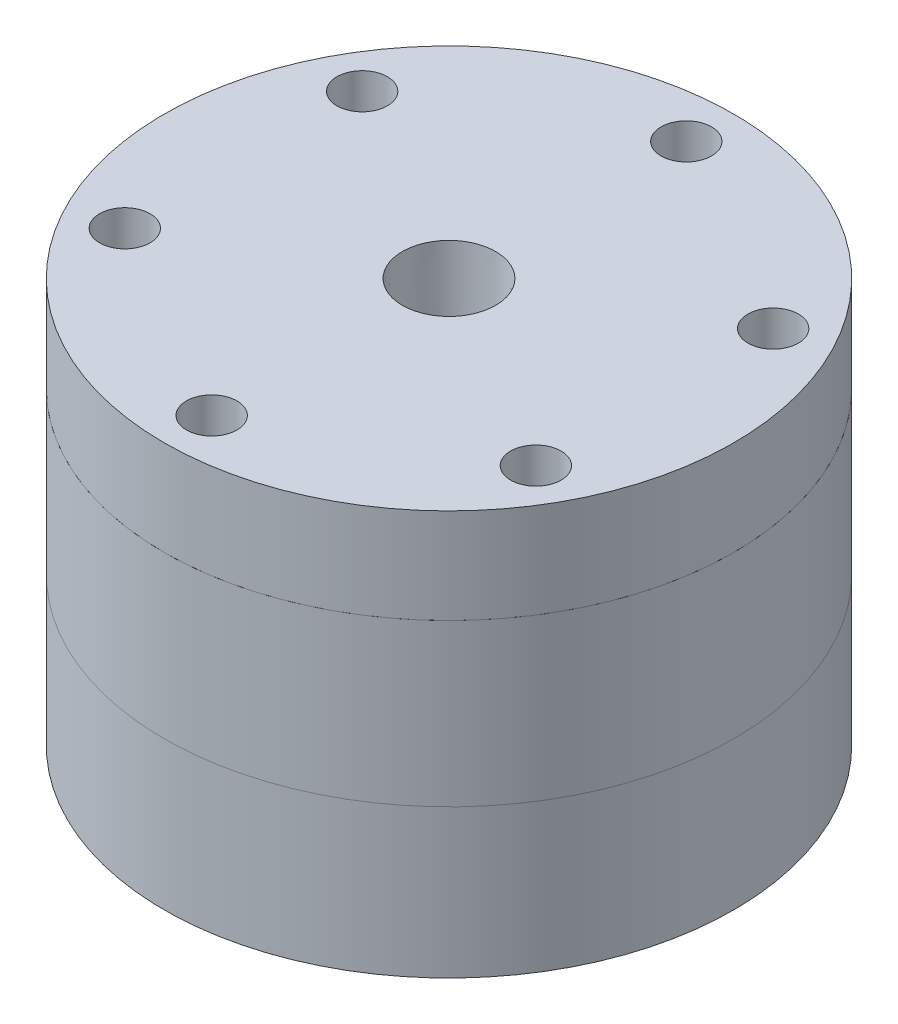
SolidWorks part; units mm, degrees
material "6061-T6 (SS)"
ref_plane "Front Plane" through (0, 0, 0) normal (0, 0, 1) x (1, 0, 0)
ref_plane "Top Plane" through (0, 0, 0) normal (0, 1, 0) x (1, 0, 0)
ref_plane "Right Plane" through (0, 0, 0) normal (1, 0, 0) x (0, 0, -1)
ref_axis "Axis1" through (0, -86.75, 0) along (0, 1, 0)
sketch "Sketch1" plane through (0, 0, 0) normal (0, 0, 1) x (1, 0, 0)
  line L12 (-25.5524, 0) -> (-38.1, 0)
  line L13 (-25.5524, 0) -> (-25.5524, -2.6924)
  line L14 (-25.5524, -2.6924) -> (-21.4884, -2.6924)
  line L15 (-21.4884, -2.6924) -> (-21.4884, 0)
  line L16 (-21.4884, 0) -> (-15.875, 0)
  line L18 (-15.875, 0) -> (-15.875, -15.24)
  line L35 (-38.1, -21.59) -> (-38.1, 0)
  line L36 (0, -86.75) -> (0, 23.25) construction
  line L37 (-15.875, -15.24) -> (-10.795, -15.24)
  line L38 (-10.795, -15.24) -> (-7.62, -18.415)
  line L39 (-7.62, -18.415) -> (-7.62, -21.59)
  line L40 (-7.62, -21.59) -> (-8.9027, -21.59)
  line L41 (-8.9027, -21.59) -> (-8.9027, -19.6088)
  line L42 (-8.9027, -19.6088) -> (-11.9761, -19.6088)
  line L43 (-11.9761, -19.6088) -> (-11.9761, -21.59)
  line L44 (-11.9761, -21.59) -> (-21.4884, -21.59)
  line L45 (-21.4884, -21.59) -> (-21.4884, -18.8976)
  line L46 (-21.4884, -18.8976) -> (-25.5524, -18.8976)
  line L47 (-25.5524, -18.8976) -> (-25.5524, -21.59)
  line L48 (-25.5524, -21.59) -> (-38.1, -21.59)
  dimension "D2" = 1.9812
  dimension "D3" = 15.24
  dimension "D4" = 15.875
  dimension "D5" = 38.1
  dimension "D6" = 25.5524
  dimension "D7" = 3.0734
  dimension "D8" = 11.9761
  dimension "D9" = 7.62
  dimension "D10" = 135
  dimension "D11" = 4.064
  dimension "D12" = 2.6924
  dimension "D13" = 6.35
  dimension "D14" = 3.175
  dimension "D15" = 2.6924
  dimension "D16" = 4.064
revolve "Revolve1" add sketch "Sketch1" angle 360 about axis through (0, -86.75, 0) along (0, 1, 0)
sketch "Sketch21" plane through (0, 0, 0) normal (0, 0, 1) x (1, 0, 0)
  line L19 (-38.1, -35.0774) -> (-38.1, -21.59)
  line L20 (-38.1, -21.59) -> (-19.05, -21.59)
  line L21 (-11.9761, -21.59) -> (-21.4884, -21.59) construction
  line L22 (-19.05, -21.59) -> (-19.05, -35.0774)
  line L25 (-19.05, -35.0774) -> (-38.1, -35.0774)
  line L26 (0, -86.75) -> (0, 23.25) construction
  dimension "D1" = 19.05
  dimension "D3" = 13.4874
revolve "Revolve7" add sketch "Sketch21" angle 360 about axis through (0, -86.75, 0) along (0, 1, 0)
sketch "Sketch4" plane through (0, 0, 0) normal (0, 0, 1) x (1, 0, 0)
  line L0 (-6.35, -35.0774) -> (-38.1, -35.0774)
  line L3 (-11.1125, -41.4274) -> (-6.35, -36.6649)
  line L6 (-38.1, -41.4274) -> (-11.1125, -41.4274)
  line L7 (-6.35, -36.6649) -> (-6.35, -35.0774)
  line L8 (0, -86.75) -> (0, 23.25) construction
  line L9 (-38.1, -41.4274) -> (-38.1, -35.0774)
  dimension "D1" = 6.35
  dimension "D2" = 6.35
  dimension "D3" = 135
  dimension "D4" = 1.5875
revolve "Revolve5" add sketch "Sketch4" angle 360 about axis through (0, -86.75, 0) along (0, 1, 0)
sketch "Sketch13" plane through (0, 0, 0) normal (0, 1, 0) x (1, 0, 0)
  circle A0 centre (0, 0) radius 38.1
extrude "Boss-Extrude1" add sketch "Sketch13" along normal blind 12.7 separate body
ref_plane "Plane1" through (-38.1, 0, 0) normal (-1, 0, 0) x (0, 0, 1)
hole_wizard "1/4 NPT Tapped Hole3" positions "Sketch9" profile "Sketch10" size "1/4" standard "ANSI Inch"
sketch "Sketch9" plane through (-38.1, 0, 0) normal (-1, 0, 0) x (0, 0, 1)
  line L0 (0, -86.75) -> (0, 23.25) construction
  line L2 (0, -35.0774) -> (0, -21.59) construction
  point P0 (0, -30.6324)
  dimension "D1" = 4.445
sketch "Sketch10" plane through (-38.1, -30.6324, 0) normal (0, 1, 0) x (0, 0, 1)
  line L0 (0, 0) -> (0, 25.6943)
  line L1 (5.5626, 22.352) -> (0, 25.6943)
  line L2 (-5.5626, 22.352) -> (0, 25.6943) construction
  line L3 (5.5626, 22.352) -> (5.5626, 9.906)
  line L4 (5.5626, 9.906) -> (5.9437, 9.906)
  line L5 (5.9437, 9.906) -> (6.2403, 0)
  line L6 (-5.9437, 9.906) -> (-6.2403, 0) construction
  line L7 (6.2403, 0) -> (0, 0)
  line L8 (0, -6.35) -> (0, 107.95) construction
  line L11 (-5.5626, 9.906) -> (-5.9437, 9.906) construction
  dimension "Tap Drill Dia." = 11.1252
  dimension "Tap Drill Depth" = 22.352
  dimension "Thread Dia." = 12.4806
  dimension "Thread Angle" = 3.43
  dimension "Thread Depth" = 9.906
  dimension "Drill Angle" = 118
cosmetic thread "Hole Thread4" parameters "D1"=9.906, "D2"=13.7086
hole_wizard "1/4 NPT Tapped Hole4" positions "Sketch16" profile "Sketch17" size "1/4" standard "ANSI Inch" end condition through all
sketch "Sketch16" plane through (0, 12.7, 0) normal (0, 1, 0) x (1, 0, 0)
  point P0 (0, 0)
sketch "Sketch17" plane through (0, 12.7, 0) normal (1, 0, 0) x (0, 0, 1)
  line L0 (0, 0) -> (0, 54.1274)
  line L1 (0, 54.1274) -> (5.5626, 54.1274)
  line L2 (-5.9437, 9.906) -> (-6.2403, 0) construction
  line L3 (5.5626, 54.1274) -> (5.5626, 9.906)
  line L4 (5.5626, 9.906) -> (5.9437, 9.906)
  line L5 (5.9437, 9.906) -> (6.2403, 0)
  line L7 (6.2403, 0) -> (0, 0)
  line L8 (0, -6.35) -> (0, 107.95) construction
  line L11 (-5.5626, 9.906) -> (-5.9437, 9.906) construction
  dimension "Thru Tap Drill Dia." = 11.1252
  dimension "Thru Tap Drill Depth" = 54.1274
  dimension "Thread Dia." = 12.4806
  dimension "Thread Angle" = 3.43
  dimension "Thread Depth" = 9.906
cosmetic thread "Hole Thread3" parameters "D1"=9.906, "D2"=13.7086
hole_wizard "1/4 Clearance Hole1" positions "Sketch14" profile "Sketch15" hole size "1/4" standard "ANSI Inch" end condition through all
sketch "Sketch14" plane through (0, 12.7, 0) normal (0, 1, 0) x (1, 0, 0)
  line L0 (0, 0) -> (-45.4895, 0) construction
  line L2 (0, 0) -> (-27.4963, 15.875) construction
  point P0 (-27.4963, 15.875)
  dimension "D1" = 30
  dimension "D2" = 31.75
sketch "Sketch15" plane through (-27.4963, 12.7, -15.875) normal (1, 0, 0) x (0, 0, 1)
  line L0 (0, 0) -> (0, 54.1274)
  line L1 (0, 54.1274) -> (3.3782, 54.1274)
  line L2 (3.3782, 54.1274) -> (3.3782, 0)
  line L5 (3.3782, 0) -> (0, 0)
  line L11 (0, -6.35) -> (0, 107.95) construction
  dimension "Thru Hole Dia." = 6.7564
  dimension "Thru Hole Depth" = 54.1274
pattern_circular "CirPattern1" count 6 over 360 about axis through (0, 0, 0) along (0, 1, 0) of "1/4 Clearance Hole1"
